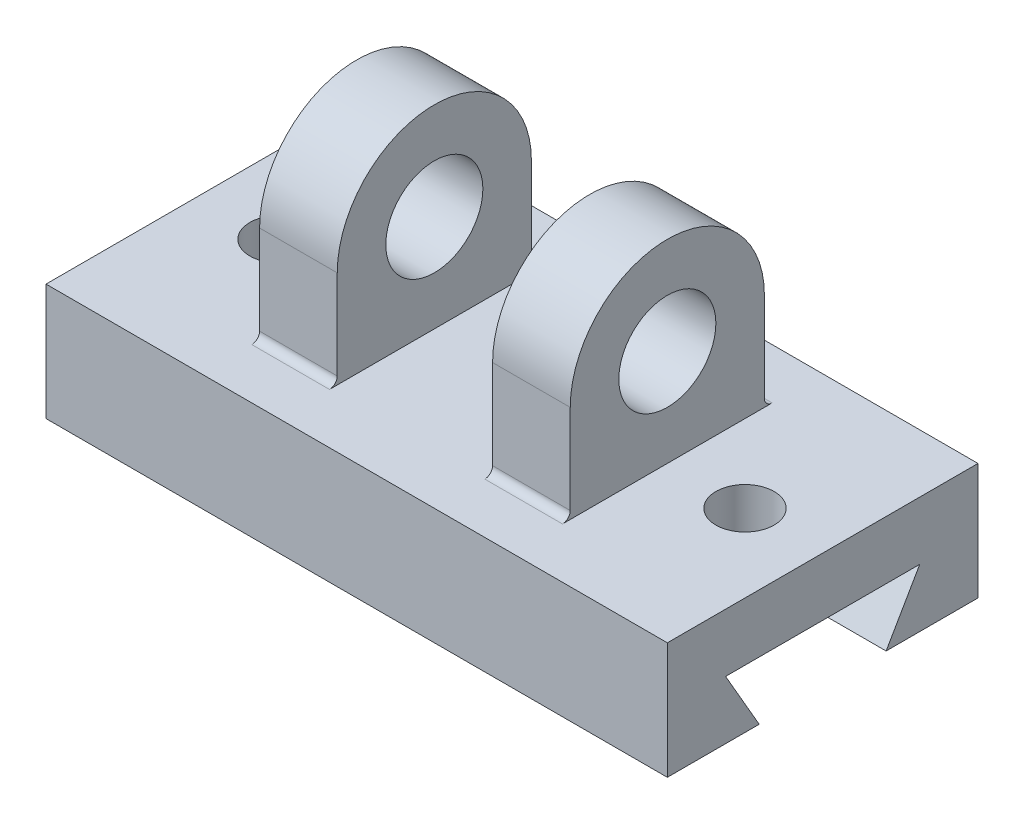
SolidWorks part; units mm, degrees
material "1060 Alloy"
ref_plane "Front Plane" through (0, 0, 0) normal (0, 0, 1) x (1, 0, 0)
ref_plane "Top Plane" through (0, 0, 0) normal (0, 1, 0) x (1, 0, 0)
ref_plane "Right Plane" through (0, 0, 0) normal (1, 0, 0) x (0, 0, -1)
sketch "Sketch1" plane through (0, 0, 0) normal (1, 0, 0) x (0, 0, -1)
  line L0 (-65, -15) -> (-15, -15)
  line L1 (0, 0) -> (-80, 0)
  line L2 (0, 0) -> (0, -30)
  line L3 (0, -30) -> (-23.6603, -30)
  line L4 (-80, 0) -> (-80, -30)
  line L5 (-65, -15) -> (-56.3397, -30)
  line L6 (-15, -15) -> (-23.6603, -30)
  line L7 (-56.3397, -30) -> (-80, -30)
  dimension "D1" = 30
  dimension "D2" = 80
  dimension "D3" = 15
  dimension "D4" = 15
  dimension "D5" = 15
  dimension "D6" = 60
  dimension "D7" = 60
sketch "Sketch2" plane through (0, 0, 0) normal (1, 0, 0) x (0, 0, -1)
extrude "Boss-Extrude1" add sketch "Sketch1" along normal blind 80
sketch "Sketch4" plane through (0, 0, 0) normal (0, 1, 0) x (1, 0, 0)
  line L0 (0, 0) -> (0, -80) construction
  line L1 (20, -15) -> (40, -15)
  line L2 (20, -15) -> (20, -65)
  line L3 (20, -65) -> (40, -65)
  line L4 (40, -15) -> (40, -65)
  line L5 (80, -80) -> (0, -80) construction
  point P10 (20, -40)
  dimension "D1" = 20
  dimension "D4" = 40
  dimension "D5" = 50
  dimension "D7" = 20
extrude "Boss-Extrude2" add sketch "Sketch4" along normal blind 50
sketch "Sketch5" plane through (0, 0, 0) normal (0, 1, 0) x (1, 0, 0)
  line L0 (40, -65) -> (40, -15) construction
  circle A0 centre (60, -40) radius 7.5
  point P4 (40, -40)
  dimension "D1" = 15
  dimension "D2" = 20
  dimension "D3" = 0
extrude "Cut-Extrude2" cut sketch "Sketch5" against normal blind 15
sketch "Sketch9" plane through (0, 0, 0) normal (1, 0, 0) x (0, 0, -1)
  line L1 (-65, 50) -> (-65, 0) construction
  line L3 (-65, 25) -> (-65, 50)
  line L4 (-65, 50) -> (-40, 50)
  arc A0 (-40, 50) -> (-65, 25) centre (-40, 25) ccw
sketch "Sketch10" plane through (0, 0, 0) normal (1, 0, 0) x (0, 0, -1)
extrude "Cut-Extrude3" cut sketch "Sketch9" along normal blind 40
sketch "Sketch11" plane through (0, 0, 0) normal (1, 0, 0) x (0, 0, -1)
  line L0 (-15, 25) -> (-15, 50)
  line L1 (-15, 50) -> (-15, 0) construction
  line L2 (-15, 50) -> (-40, 50)
  arc A0 (-40, 50) -> (-15, 25) centre (-40, 25) cw
extrude "Cut-Extrude4" cut sketch "Sketch11" along normal blind 40
sketch "Sketch13" plane through (0, 0, 0) normal (1, 0, 0) x (0, 0, -1)
  line L0 (-65, 0) -> (-15, 0) construction
  line L1 (-15, 25) -> (-15, 0) construction
  circle A0 centre (-40, 25) radius 12.5
  dimension "D1" = 25
  dimension "D2" = 25
  dimension "D3" = 25
extrude "Cut-Extrude5" cut sketch "Sketch13" along normal blind 40
mirror "Mirror3" about plane through (0, 0, 0) normal (1, 0, 0) of "Cut-Extrude5", "Cut-Extrude2", "Boss-Extrude2", "Cut-Extrude3", "Boss-Extrude1"
sketch "Sketch17" plane through (-20, 0, 0) normal (1, 0, 0) x (0, 0, -1)
  line L0 (-40, 50) -> (-15, 50)
  line L1 (-15, 50) -> (-15, 25)
  line L2 (-15, 50) -> (-15, 0) construction
  arc A0 (-15, 25) -> (-65, 25) centre (-40, 25) ccw construction
  arc A1 (-15, 25) -> (-40, 50) centre (-40, 25) ccw
extrude "Cut-Extrude6" cut sketch "Sketch17" against normal blind 20
fillet "Fillet1" radius 2 4 edges at (-30, 0, 15) (30, 0, 15) (30, 0, 65) (-30, 0, 65)
